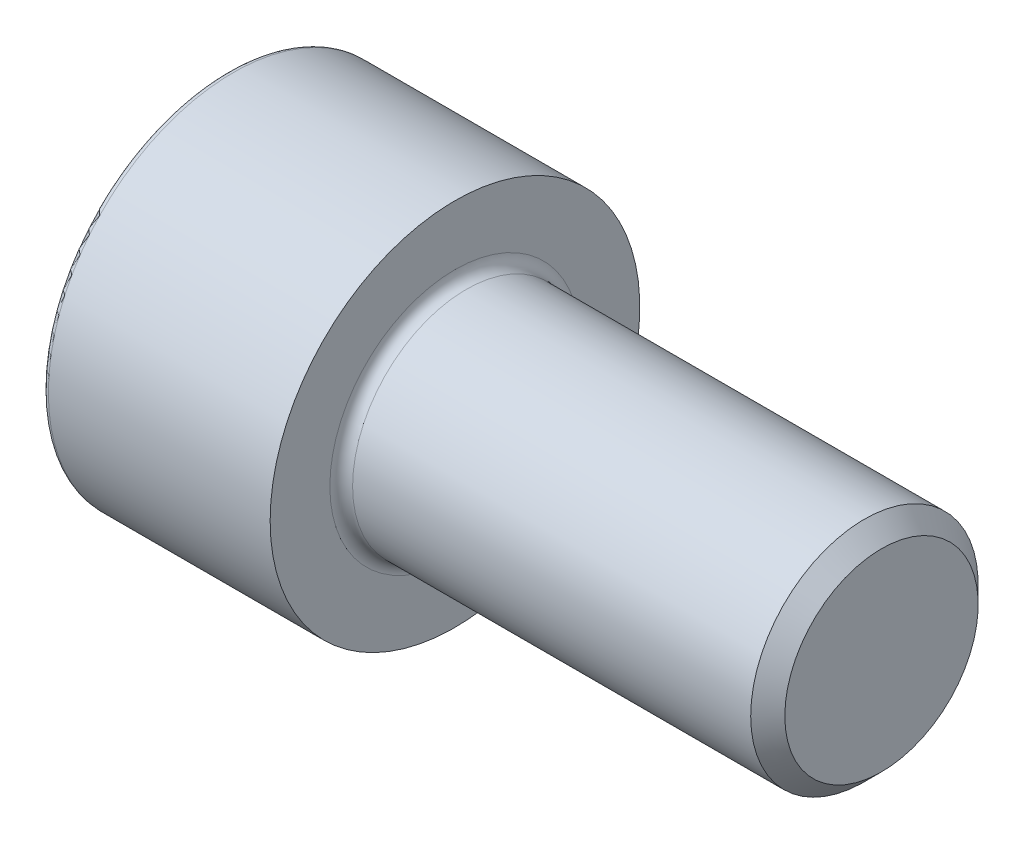
SolidWorks part; units mm, degrees
ref_plane "Front Plane" through (0, 0, 0) normal (0, 0, 1) x (1, 0, 0)
ref_plane "Top Plane" through (0, 0, 0) normal (0, 1, 0) x (1, 0, 0)
ref_plane "Right Plane" through (0, 0, 0) normal (1, 0, 0) x (0, 0, -1)
sketch "草图1" plane through (0, 0, 0) normal (0, 0, 1) x (1, 0, 0)
  line L0 (0, 0) -> (85.0281, 0) construction
  line L1 (0, 0) -> (0, 6.5)
  line L2 (0, 6.5) -> (8, 6.5)
  line L3 (8, 6.5) -> (8, 4)
  line L4 (8, 4) -> (23, 4)
  line L5 (23, 4) -> (23, 0)
  line L6 (23, 0) -> (0, 0)
  dimension "D1" = 8
  dimension "D2" = 13
  dimension "D3" = 8
  dimension "D4" = 15
revolve "旋转1" add sketch "草图1" angle 360 about L0
hole_wizard "大小mm 暗销孔1" positions "草图3" profile "草图2" hole size "Ø6.0" standard "GB"
sketch "草图3" plane through (0, 0, 0) normal (-1, 0, 0) x (0, 0, 1)
  point P0 (0, 0)
sketch "草图2" plane through (0, 0, 0) normal (0, 1, 0) x (0, 0, 1)
  line L0 (0, 0) -> (0, 5.8026)
  line L1 (0, 5.8026) -> (3, 4)
  line L2 (3, 4) -> (3, 0)
  line L5 (3, 0) -> (0, 0)
  line L10 (0, 5.8026) -> (-3, 4) construction
  line L11 (0, -6.35) -> (0, 107.95) construction
  dimension "孔直径" = 6
  dimension "孔深度" = 4
  dimension "导头角度" = 118
sketch "草图4" plane through (0, 0, 0) normal (-1, 0, 0) x (0, 0, 1)
  line L0 (0, 3.4641) -> (0, -3.4641) construction
  line L1 (3, 1.7321) -> (0, 3.4641)
  line L2 (0, 3.4641) -> (-3, 1.7321)
  line L3 (-3, 1.7321) -> (-3, -1.7321)
  line L4 (-3, -1.7321) -> (0, -3.4641)
  line L5 (0, -3.4641) -> (3, -1.7321)
  line L6 (3, -1.7321) -> (3, 1.7321)
  circle A0 centre (0, 0) radius 3 construction
  dimension "D1" = 6
extrude "切除-拉伸1" cut sketch "草图4" against normal blind 4
fillet "圆角1" radius 0.2 1 edges at (0, 0, 6.5)
chamfer "倒角1" distance 0.6 angle 45 1 edges at (23, 0, 4)
fillet "圆角2" radius 0.4 1 edges at (8, 0, 4)
